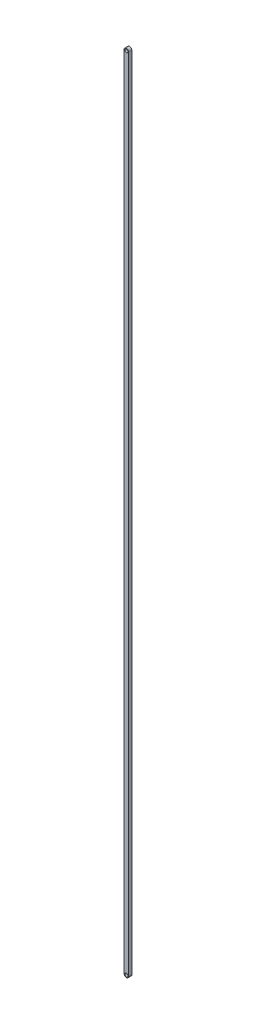
SolidWorks part; units mm, degrees
ref_plane "Front Plane" through (0, 0, 0) normal (0, 0, 1) x (1, 0, 0)
ref_plane "Top Plane" through (0, 0, 0) normal (0, 1, 0) x (1, 0, 0)
ref_plane "Right Plane" through (0, 0, 0) normal (1, 0, 0) x (0, 0, -1)
sketch "Sketch2" plane through (0, 0, 0) normal (0, 0, 1) x (1, 0, 0)
  line L0 (0, 0) -> (0, -1244) construction
  line L1 (3.5, 0) -> (3.5, -1244)
  line L2 (-3.5, 0) -> (-3.5, -1244)
  arc A0 (3.5, 0) -> (-3.5, 0) centre (0, 0) ccw
  arc A1 (-3.5, -1244) -> (3.5, -1244) centre (0, -1244) ccw
  circle A2 centre (0, 0) radius 2.5
  circle A3 centre (0, -1244) radius 2.5
  point P3 (0, -622)
  dimension "D2" = 5
  dimension "D3" = 3.5
  dimension "D1" = 1244
extrude "Boss-Extrude1" add sketch "Sketch2" along normal mid plane 5
